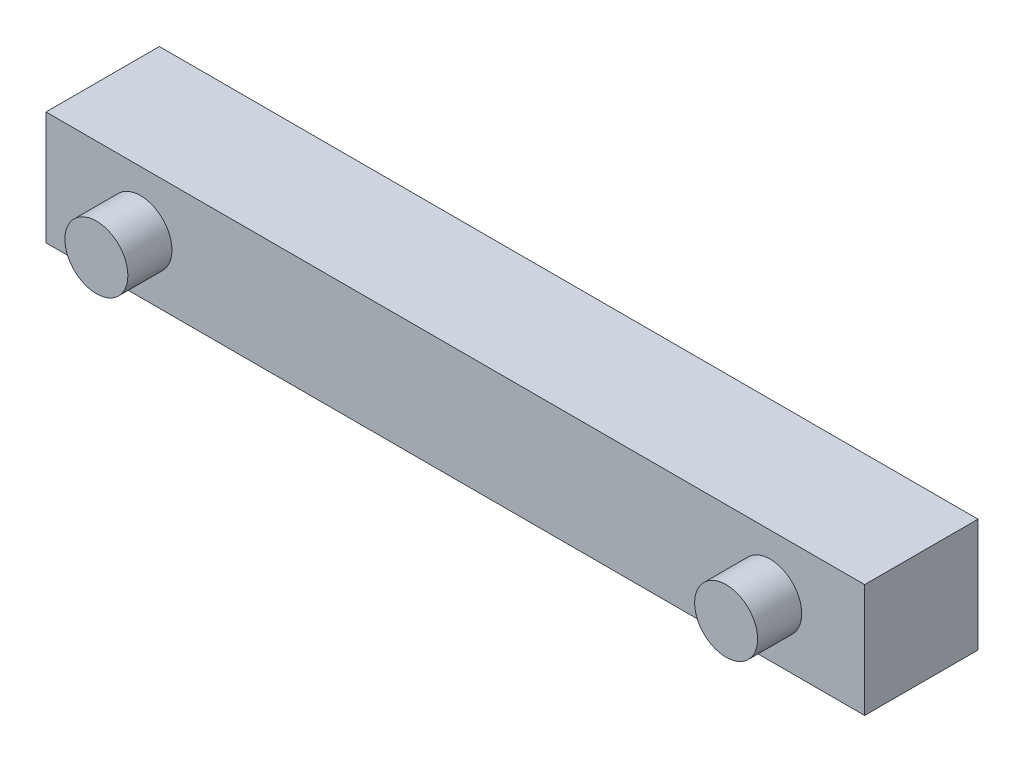
SolidWorks part; units mm, degrees
ref_plane "Front Plane" through (0, 0, 0) normal (0, 0, 1) x (1, 0, 0)
ref_plane "Top Plane" through (0, 0, 0) normal (0, 1, 0) x (1, 0, 0)
ref_plane "Right Plane" through (0, 0, 0) normal (1, 0, 0) x (0, 0, -1)
sketch "Sketch1" plane through (0, 0, 0) normal (0, 0, 1) x (1, 0, 0)
  line L0 (0, 4.5) -> (73.4691, 4.5) construction
  line L1 (0, 0) -> (65, 0)
  line L2 (0, 0) -> (0, 9)
  line L3 (0, 9) -> (65, 9)
  line L4 (65, 0) -> (65, 9)
  line L5 (73.4691, 4.5) -> (-9.7375, 4.5) construction
  dimension "D1" = 65
  dimension "D2" = 9
extrude "Boss-Extrude4" add sketch "Sketch1" along normal blind 9
sketch "Sketch5" plane through (0, 0, 9) normal (0, 0, 1) x (1, 0, 0)
  line L0 (32.5, 9) -> (32.5, 0) construction
  line L1 (65, 9) -> (0, 9) construction
  line L2 (0, 0) -> (65, 0) construction
  line L3 (32.5, 4.5) -> (57.5, 4.5) construction
  line L4 (32.5, 4.5) -> (7.5, 4.5) construction
  circle A0 centre (7.5, 4.5) radius 2.5
  circle A1 centre (57.5, 4.5) radius 2.5
  dimension "5" = 2.5
  dimension "D4" = 2.5
  dimension "D1" = 25
  dimension "D2" = 25
extrude "Boss-Extrude5" add sketch "Sketch5" along normal blind 3.5
